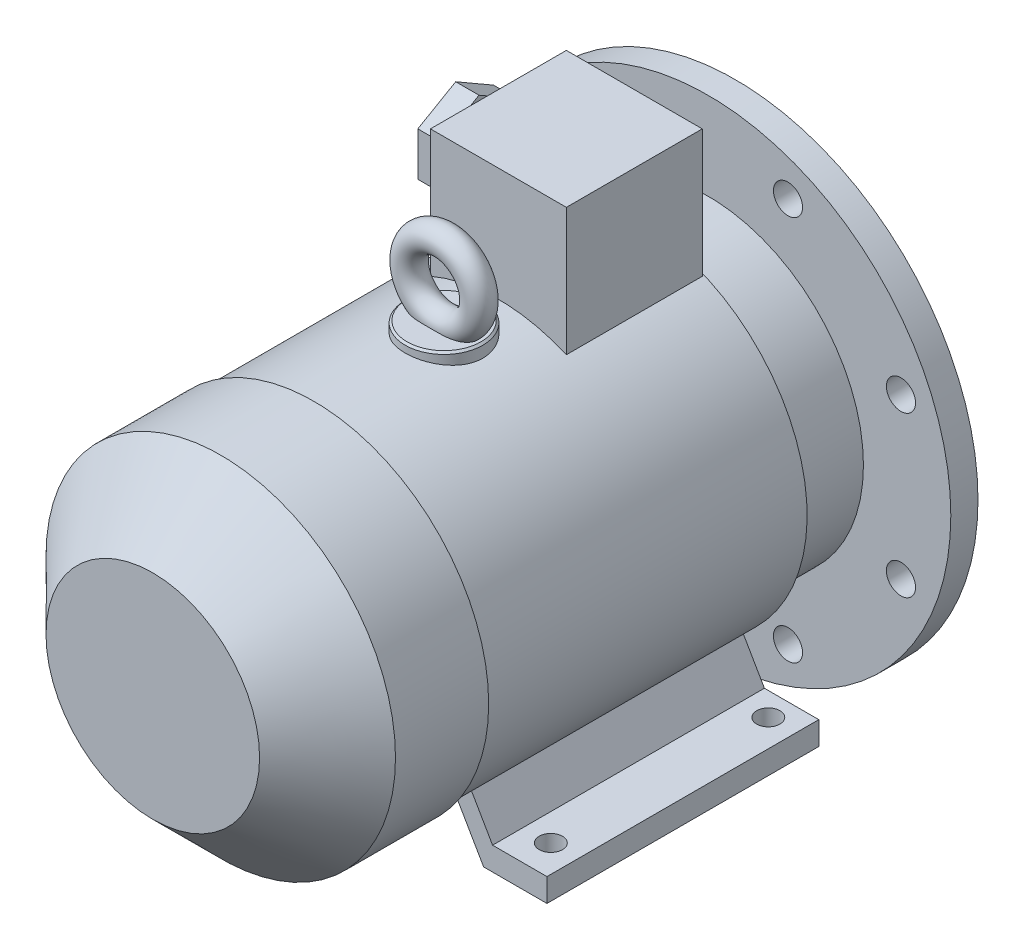
SolidWorks part; units mm, degrees
material "Ст.3 ГОСТ 380-88"
ref_plane "Спереди" through (0, 0, 0) normal (0, 0, 1) x (1, 0, 0)
ref_plane "Сверху" through (0, 0, 0) normal (0, 1, 0) x (1, 0, 0)
ref_plane "Справа" through (0, 0, 0) normal (1, 0, 0) x (0, 0, -1)
sketch "Эскиз1" plane through (0, 0, 0) normal (0, 0, 1) x (1, 0, 0)
  circle A0 centre (0, 0) radius 14
  dimension "D1" = 28
extrude "Вытянуть1" add sketch "Эскиз1" along normal blind 60
sketch "Эскиз2" plane through (0, 0, 0) normal (0, 0, -1) x (-1, 0, 0)
  line L0 (0, 0) -> (0, 16.3748) construction
  line L2 (-3.5, 17) -> (3.5, 17)
  line L3 (-3.5, 17) -> (-3.5, 10)
  line L4 (-3.5, 10) -> (3.5, 10)
  line L5 (3.5, 17) -> (3.5, 10)
  circle A2 centre (0, 0) radius 14 construction
  dimension "D1" = 7
  dimension "D2" = 7
  dimension "D3" = 31
extrude "Вытянуть2" add sketch "Эскиз2" against normal blind 30 and the other way blind 0.1
sketch "Эскиз3" plane through (0, 0, 60) normal (0, 0, 1) x (1, 0, 0)
  circle A0 centre (0, 0) radius 125
  dimension "D1" = 250
extrude "Вытянуть3" add sketch "Эскиз3" along normal blind 14
sketch "Эскиз4" plane through (0, 0, 60) normal (0, 0, -1) x (-1, 0, 0)
  circle A0 centre (0, 0) radius 90
  circle A1 centre (0, 0) radius 85
  dimension "D1" = 180
  dimension "D2" = 170
extrude "Вытянуть4" add sketch "Эскиз4" along normal blind 4
sketch "Эскиз5" plane through (0, 0, 60) normal (0, 0, -1) x (-1, 0, 0)
  circle A0 centre (0, 0) radius 85
  circle A1 centre (0, 0) radius 25
  dimension "D1" = 170
  dimension "D2" = 50
extrude "Вырез-Вытянуть1" cut sketch "Эскиз5" against normal blind 8
chamfer "Фаска1" distance 1 angle 45 3 edges at (-90, 0, 56) (-25, 0, 60) (0, -14, 0)
sketch "Эскиз6" plane through (0, 0, 60) normal (0, 0, -1) x (-1, 0, 0)
  line L0 (0, 0) -> (0, 142.5846) construction
  line L1 (0, 0) -> (-57.2161, 138.132) construction
  circle A0 centre (-41.1385, 99.317) radius 7.5
  circle A6 centre (41.1385, 99.317) radius 7.5
  circle A7 centre (99.317, 41.1385) radius 7.5
  circle A8 centre (99.317, -41.1385) radius 7.5
  circle A9 centre (41.1385, -99.317) radius 7.5
  circle A10 centre (-41.1385, -99.317) radius 7.5
  circle A11 centre (-99.317, -41.1385) radius 7.5
  circle A12 centre (-99.317, 41.1385) radius 7.5
  dimension "D2" = 15
  dimension "D1" = 22.5
  dimension "D3" = 107.5
  dimension "D4" = 107.5
  dimension "D5" = 107.5
extrude "Вырез-Вытянуть2" cut sketch "Эскиз6" against normal through all
sketch "Эскиз7" plane through (0, 0, 74) normal (0, 0, 1) x (1, 0, 0)
  circle A0 centre (0, 0) radius 80
  dimension "D1" = 160
extrude "Вытянуть5" add sketch "Эскиз7" along normal blind 37
sketch "Эскиз8" plane through (0, 0, 111) normal (0, 0, 1) x (1, 0, 0)
  circle A0 centre (0, 0) radius 88
  dimension "D1" = 176
extrude "Вытянуть6" add sketch "Эскиз8" along normal blind 166
sketch "Эскиз9" plane through (0, 0, 277) normal (0, 0, 1) x (1, 0, 0)
  circle A0 centre (0, 0) radius 90
  dimension "D1" = 180
extrude "Вытянуть7" add sketch "Эскиз9" along normal blind 83
chamfer "Фаска2" distance 35 angle 45 1 edges at (90, 0, 360)
sketch "Эскиз10" plane through (0, 0, 111) normal (0, 0, -1) x (-1, 0, 0)
  line L0 (0, 0) -> (0, -143.0671) construction
  line L1 (-94, -100) -> (-61.3812, -100)
  line L2 (-61.3812, -100) -> (-42.2846, -66.9238)
  line L3 (-42.2846, -66.9238) -> (-50.9449, -61.9238)
  line L4 (-50.9449, -61.9238) -> (-66, -88)
  line L5 (-66, -88) -> (-94, -88)
  line L6 (-94, -88) -> (-94, -100)
  line L7 (61.3812, -100) -> (42.2846, -66.9238)
  line L8 (94, -100) -> (61.3812, -100)
  line L9 (94, -88) -> (94, -100)
  line L10 (66, -88) -> (94, -88)
  line L11 (50.9449, -61.9238) -> (66, -88)
  line L12 (42.2846, -66.9238) -> (50.9449, -61.9238)
  dimension "D1" = 12
  dimension "D2" = 94
  dimension "D3" = 28
  dimension "D4" = 10
  dimension "D5" = 30
  dimension "D6" = 100
extrude "Вытянуть8" add sketch "Эскиз10" against normal blind 140
sketch "Эскиз11" plane through (0, -100, 0) normal (0, -1, 0) x (1, 0, 0)
  line L0 (-146.997, 123) -> (126.8414, 123) construction
  line L2 (-80, 123) -> (80, 123) construction
  line L3 (-80, 123) -> (-80, 235) construction
  circle A0 centre (-80, 123) radius 6
  circle A1 centre (80, 123) radius 6
  circle A2 centre (-80, 235) radius 6
  circle A3 centre (80, 235) radius 6
  dimension "D2" = 12
  dimension "D1" = 123
  dimension "D3" = 80
  dimension "D4" = 90
  dimension "D5" = 160
  dimension "D6" = 112
  dimension "D7" = 112
  dimension "D8" = 235
extrude "Вырез-Вытянуть3" cut sketch "Эскиз11" against normal up to next
sketch "Эскиз12" plane through (0, 0, 0) normal (0, 1, 0) x (1, 0, 0)
  line L0 (0, 0) -> (0, -371.4753) construction
  line L1 (88, -111) -> (-88, -111) construction
  line L2 (-35, -112) -> (35, -112)
  line L3 (-35, -112) -> (-35, -182)
  line L4 (-35, -182) -> (35, -182)
  line L5 (35, -112) -> (35, -182)
  dimension "D1" = 70
  dimension "D2" = 70
  dimension "D3" = 1
extrude "Вытянуть9" add sketch "Эскиз12" along normal blind 146.5
sketch "Эскиз13" plane through (0, 0, 0) normal (0, 1, 0) x (1, 0, 0)
  line L0 (0, 0) -> (0, -251.1897) construction
  circle A0 centre (0, -210) radius 20
  dimension "D1" = 210
  dimension "D2" = 40
extrude "Вытянуть10" add sketch "Эскиз13" along normal blind 92.5
chamfer "Фаска3" distance 1 angle 45 1 edges at (0, 92.5, 230)
ref_plane "Плоскость1" through (0, 0, 210) normal (0, 0, 1) x (1, 0, 0)
sketch "Эскиз14" plane through (0, 0, 210) normal (0, 0, 1) x (1, 0, 0)
  line L0 (19, 92.5) -> (-19, 92.5) construction
  line L1 (0, 0) -> (0, 170.1296) construction
  circle A0 centre (0, 110.5) radius 18
  dimension "D1" = 36
sketch "Эскиз15" plane through (0, 0, 0) normal (1, 0, 0) x (0, 0, -1)
  line L0 (-210, 0) -> (-210, 170.1296) construction
  line L1 (-210, 128.5) -> (-210, 92.5) construction
  line L2 (-191, 92.5) -> (-229, 92.5) construction
  circle A0 centre (-210, 128.5) radius 7
  dimension "D1" = 14
  dimension "D2" = 36
sweep "По траектории1" add profiles "Эскиз15" path "Эскиз14"
sketch "Эскиз16" plane through (-35, 0, 0) normal (-1, 0, 0) x (0, 0, 1)
  line L0 (112, 146.5) -> (182, 146.5) construction
  line L1 (112, 146.5) -> (112, 80.7403) construction
  circle A0 centre (147, 116.5) radius 15
  dimension "D1" = 30
  dimension "D2" = 30
  dimension "D3" = 35
extrude "Вытянуть11" add sketch "Эскиз16" along normal blind 10
sketch "Эскиз17" plane through (-45, 0, 0) normal (-1, 0, 0) x (0, 0, 1)
  line L1 (147, 139.0167) -> (127.5, 127.7583)
  line L2 (127.5, 127.7583) -> (127.5, 105.2417)
  line L3 (127.5, 105.2417) -> (147, 93.9833)
  line L4 (147, 93.9833) -> (166.5, 105.2417)
  line L5 (166.5, 105.2417) -> (166.5, 127.7583)
  line L6 (166.5, 127.7583) -> (147, 139.0167)
  line L7 (147, 116.5) -> (147, 178.2707) construction
  circle A0 centre (147, 116.5) radius 19.5 construction
  circle A1 centre (147, 116.5) radius 15 construction
  dimension "D1" = 39
extrude "Вытянуть12" add sketch "Эскиз17" along normal blind 12
sketch "Эскиз18" plane through (-57, 0, 0) normal (-1, 0, 0) x (0, 0, 1)
  circle A0 centre (147, 116.5) radius 8
  circle A1 centre (147, 116.5) radius 15 construction
  dimension "D1" = 16
extrude "Вырез-Вытянуть4" cut sketch "Эскиз18" against normal blind 12
